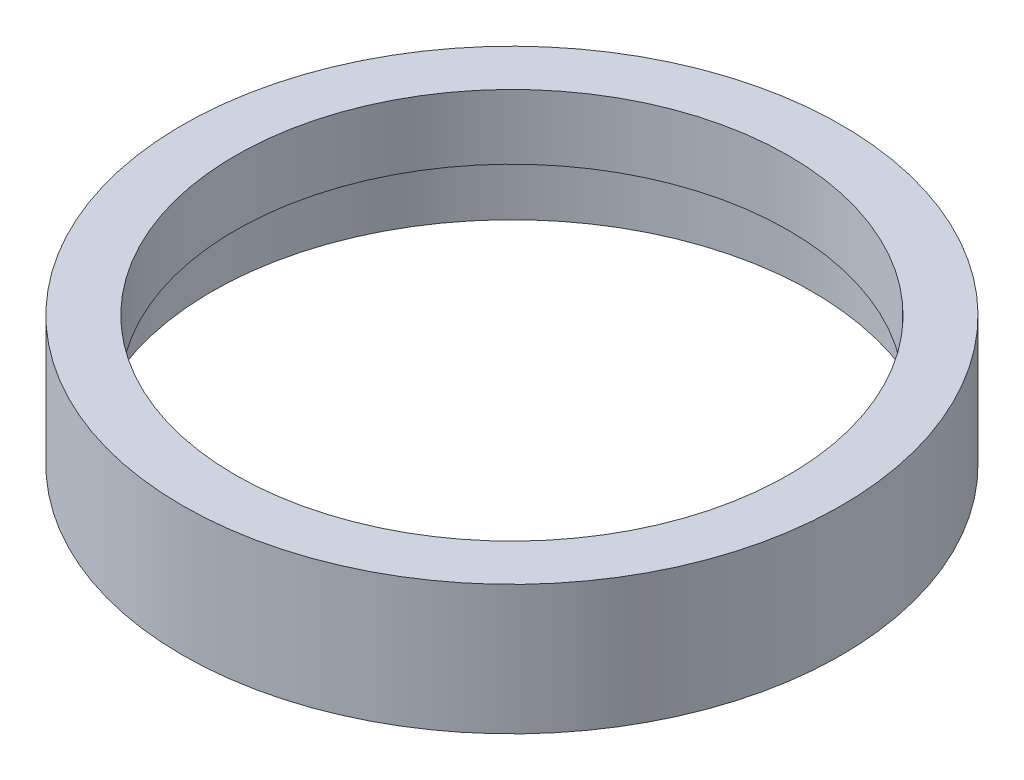
SolidWorks part; units mm, degrees
ref_plane "前视基准面" through (0, 0, 0) normal (0, 0, 1) x (1, 0, 0)
ref_plane "上视基准面" through (0, 0, 0) normal (0, 1, 0) x (1, 0, 0)
ref_plane "右视基准面" through (0, 0, 0) normal (1, 0, 0) x (0, 0, -1)
sketch "草图1" plane through (0, 0, 0) normal (0, 0, 1) x (1, 0, 0)
  line L0 (0, 60.0208) -> (0, -56.4315) construction
  line L1 (25.5, 0) -> (25.5, 4.5)
  line L2 (25.5, 4.5) -> (26.1, 4.5)
  line L3 (26.1, 4.5) -> (26.1, 5.5)
  line L4 (26.1, 5.5) -> (23.5, 5.5)
  line L5 (23.5, 5.5) -> (23.5, 11)
  line L6 (23.5, 11) -> (28, 11)
  line L7 (28, 11) -> (28, 0)
  line L8 (28, 0) -> (25.5, 0)
  point P5 (24.8, 5.5)
  dimension "D1" = 28
  dimension "D2" = 23.5
  dimension "D3" = 26.1
  dimension "D4" = 25.5
  dimension "D5" = 1
  dimension "D6" = 5.5
  dimension "D7" = 11
revolve "旋转1" add sketch "草图1" angle 360 about L0
cosmetic thread "装饰螺纹线1"
cosmetic thread "装饰螺纹线2"
